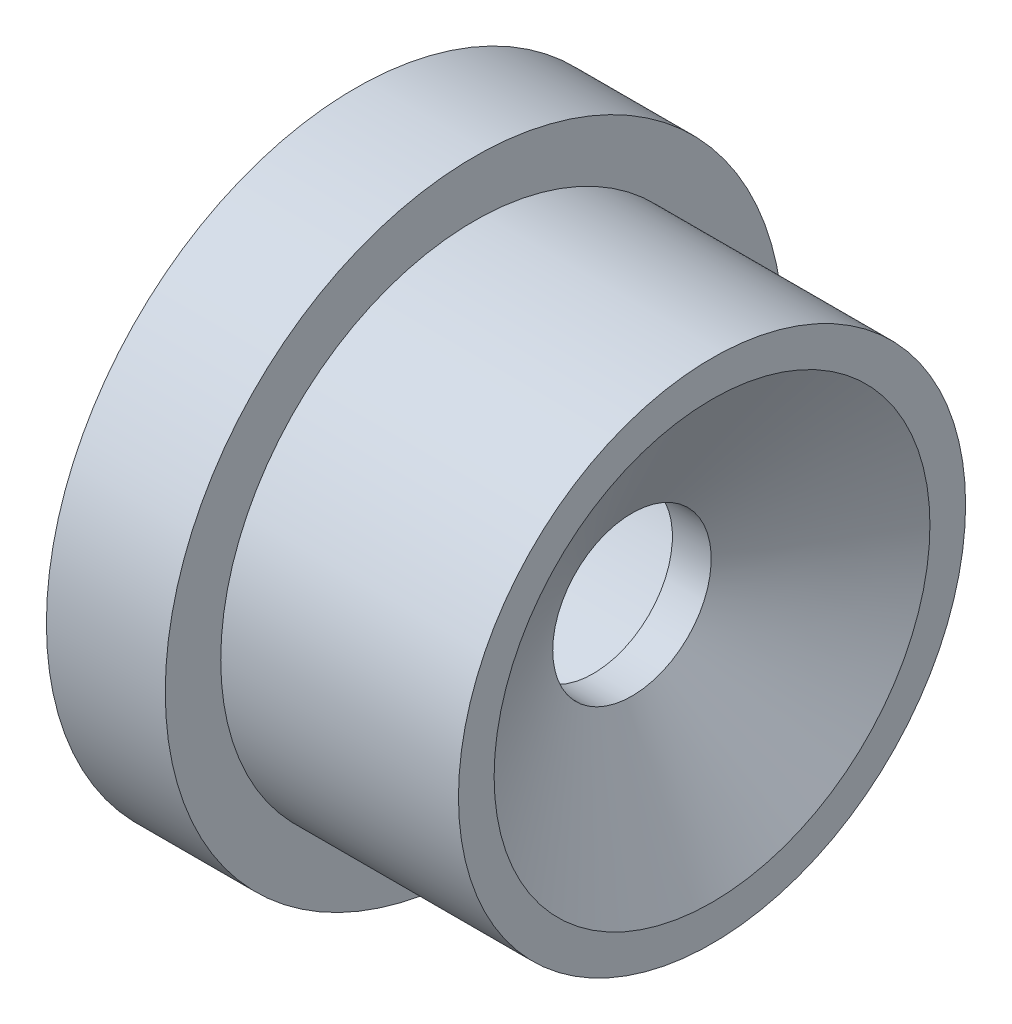
SolidWorks part; units mm, degrees
material "ПТФЭ (общий)"
ref_plane "Спереди" through (0, 0, 0) normal (0, 0, 1) x (1, 0, 0)
ref_plane "Сверху" through (0, 0, 0) normal (0, 1, 0) x (1, 0, 0)
ref_plane "Справа" through (0, 0, 0) normal (1, 0, 0) x (0, 0, -1)
sketch "Эскиз1" plane through (0, 0, 0) normal (0, 0, 1) x (1, 0, 0)
  line L0 (0, 2.25) -> (3, 2.25)
  line L1 (3, 2.25) -> (3, 1)
  line L2 (3, 1) -> (3.4896, 1)
  line L3 (3.4896, 1) -> (4.5, 2.75)
  line L4 (4.5, 2.75) -> (4.5, 3.2)
  line L5 (4.5, 3.2) -> (1.5, 3.2)
  line L6 (1.5, 3.2) -> (1.5, 3.9)
  line L7 (1.5, 3.9) -> (0, 3.9)
  line L8 (0, 3.9) -> (0, 2.25)
  line L9 (0, 0) -> (60, 0) construction
  dimension "D1" = 4.5
  dimension "D2" = 6.4
  dimension "D3" = 7.8
  dimension "D4" = 3
  dimension "D5" = 1.5
  dimension "D6" = 60
  dimension "D8" = 4.5
  dimension "D9" = 5.5
  dimension "D10" = 2
revolve "Повернуть1" add sketch "Эскиз1" angle 360 about L9
